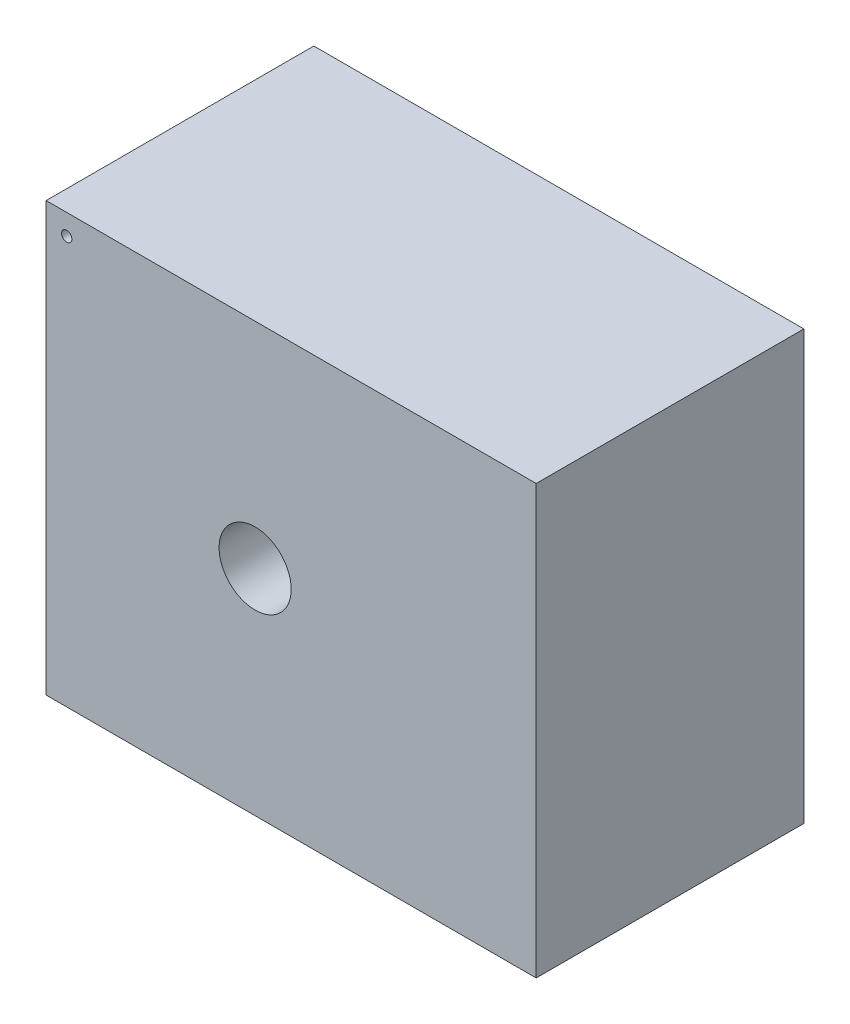
SolidWorks part; units mm, degrees
ref_plane "Front Plane" through (0, 0, 0) normal (0, 0, 1) x (1, 0, 0)
ref_plane "Top Plane" through (0, 0, 0) normal (0, 1, 0) x (1, 0, 0)
ref_plane "Right Plane" through (0, 0, 0) normal (1, 0, 0) x (0, 0, -1)
sketch "Sketch1" plane through (0, 0, 0) normal (0, 0, 1) x (1, 0, 0)
  line L4 (35, 0) -> (273, 0)
  line L5 (273, 0) -> (273, 208)
  line L6 (273, 208) -> (35, 208)
  line L7 (35, 208) -> (35, 0)
  line L8 (35, 0) -> (273, 0)
  line L9 (273, 0) -> (273, 208)
  line L10 (273, 208) -> (35, 208)
  line L11 (35, 208) -> (35, 0)
  circle A0 centre (136.5, 104) radius 17.5 construction
  circle A1 centre (136.5, 104) radius 17.5
  circle A2 centre (45, 198) radius 2.5 construction
  circle A3 centre (45, 198) radius 2.5
  dimension "D1" = 0
extrude "Boss-Extrude1" add sketch "Sketch1" against normal blind 130
